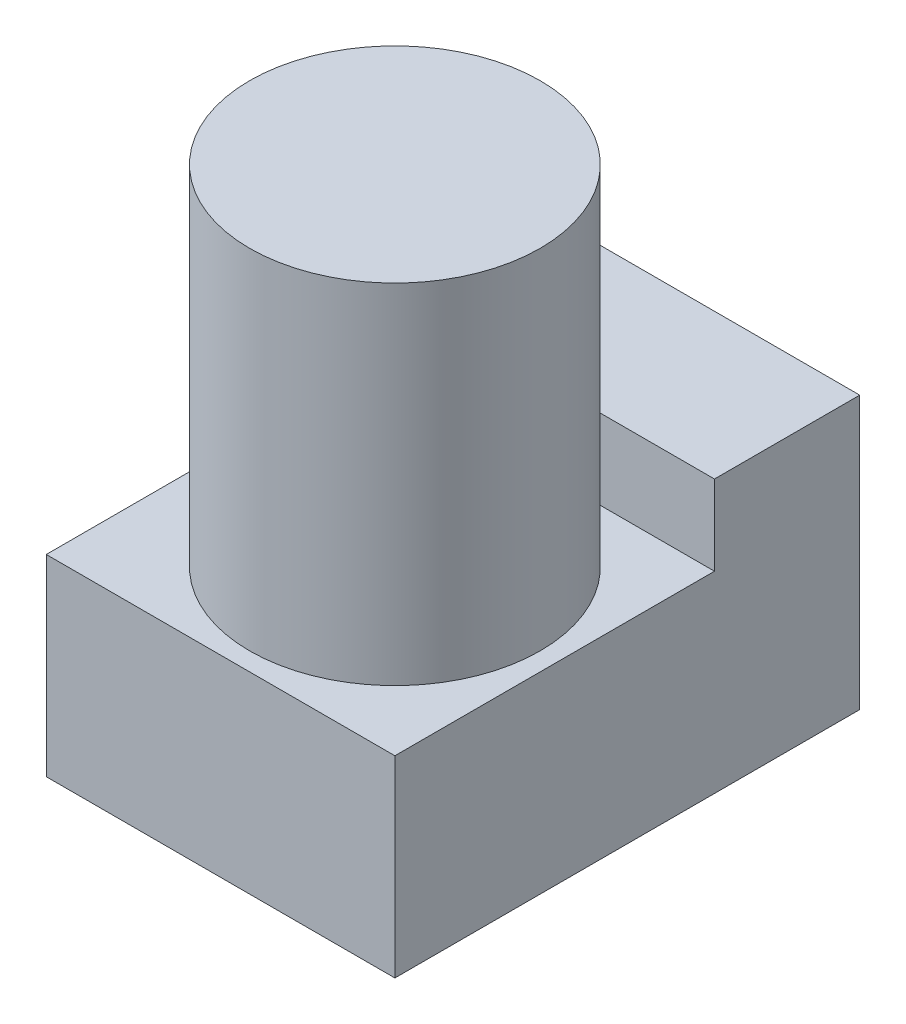
SolidWorks part; units mm, degrees
ref_plane "Plan de face" through (0, 0, 0) normal (0, 0, 1) x (1, 0, 0)
ref_plane "Plan de dessus" through (0, 0, 0) normal (0, 1, 0) x (1, 0, 0)
ref_plane "Plan de droite" through (0, 0, 0) normal (1, 0, 0) x (0, 0, -1)
sketch "Sketch1" plane through (0, 0, 0) normal (1, 0, 0) x (0, 0, -1)
  line L0 (-152.7943, -56.4036) -> (126.5507, -56.4036) construction
  line L1 (-101.4493, 123.5964) -> (-101.4493, -121.4036) construction
  line L2 (-101.4493, -56.4036) -> (26.5507, -56.4036)
  line L3 (-101.4493, -56.4036) -> (-101.4493, -3.4036)
  line L4 (-101.4493, -3.4036) -> (-13.4493, -3.4036)
  line L5 (26.5507, -56.4036) -> (26.5507, -3.4036)
  line L6 (26.5507, -3.4036) -> (26.5507, 18.5964)
  line L7 (26.5507, 18.5964) -> (-13.4493, 18.5964)
  line L8 (-13.4493, -3.4036) -> (-13.4493, 18.5964)
  dimension "D1" = 128
  dimension "D2" = 53
  dimension "D3" = 22
  dimension "D4" = 40
extrude "Boss-Extrude1" add sketch "Sketch1" along normal blind 96
sketch "Sketch2" plane through (0, -3.4036, 0) normal (0, 1, 0) x (1, 0, 0)
  line L0 (0, -56.4493) -> (96, -56.4493) construction
  circle A0 centre (51, -56.4493) radius 40
  dimension "D2" = 80
  dimension "D1" = 45
  dimension "D3" = 45
extrude "Boss-Extrude2" add sketch "Sketch2" along normal blind 96 contours A0
